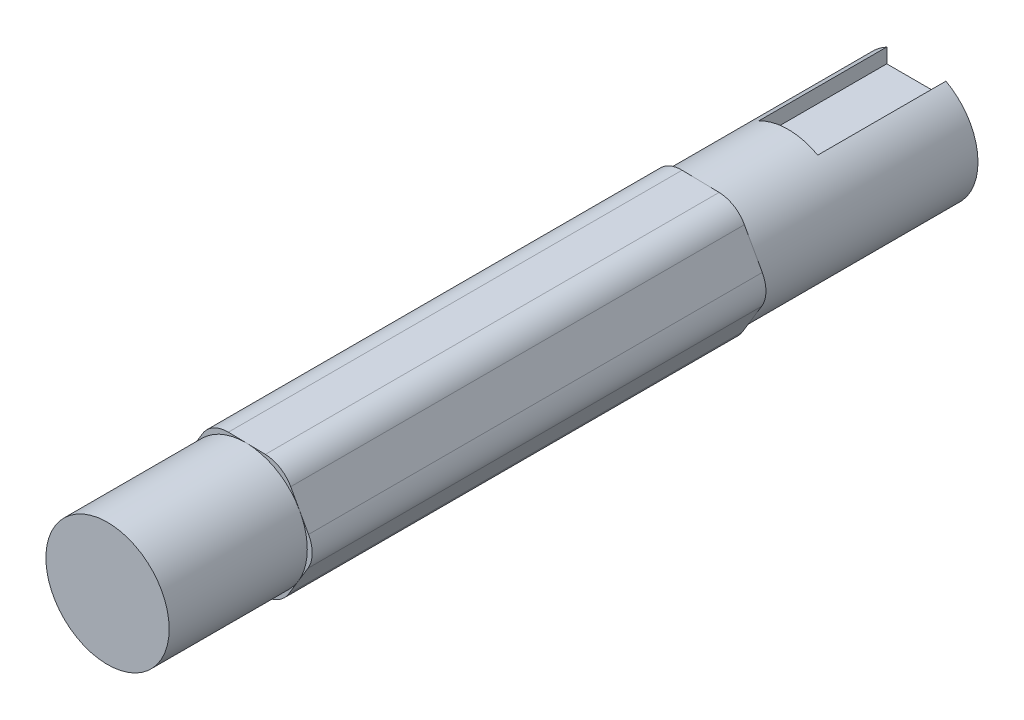
SolidWorks part; units mm, degrees
ref_plane "Front Plane" through (0, 0, 0) normal (0, 0, 1) x (1, 0, 0)
ref_plane "Top Plane" through (0, 0, 0) normal (0, 1, 0) x (1, 0, 0)
ref_plane "Right Plane" through (0, 0, 0) normal (1, 0, 0) x (0, 0, -1)
sketch "Sketch1" plane through (0, 0, 0) normal (0, 0, 1) x (1, 0, 0)
  circle A0 centre (0, 0) radius 6.25
  dimension "D1" = 12.5
extrude "Boss-Extrude1" add sketch "Sketch1" along normal blind 37 and the other way blind 45
sketch "Sketch3" plane through (0, 0, 0) normal (0, 1, 0) x (1, 0, 0)
  line L0 (-27.349, 0) -> (27.9883, 0) construction
  line L1 (-27.349, 31) -> (27.9883, 31) construction
  line L2 (-27.349, 32) -> (27.9883, 32) construction
  line L3 (-27.349, 42) -> (27.9883, 42) construction
  line L4 (27.9883, 45) -> (-27.349, 45) construction
  line L5 (-27.349, -31) -> (27.9883, -31) construction
  line L6 (-27.349, -37) -> (27.9883, -37) construction
  dimension "D1" = 31
  dimension "D2" = 1
  dimension "D3" = 10
  dimension "D4" = 3
  dimension "D5" = 31
  dimension "D6" = 6
sketch "Sketch4" plane through (0, 0, -45) normal (0, 0, -1) x (-1, 0, 0)
  line L0 (-18.2857, 6.25) -> (18.9059, 6.25) construction
  line L1 (-3, 8.5) -> (3, 8.5)
  line L2 (-3, 8.5) -> (-3, 4)
  line L3 (-3, 4) -> (3, 4)
  line L4 (3, 8.5) -> (3, 4)
  line L5 (0, 15.7597) -> (0, -12.3933) construction
  circle A0 centre (0, 0) radius 6.25 construction
  dimension "D1" = 6
  dimension "D2" = 4.5
extrude "Cut-Extrude1" cut sketch "Sketch4" against normal blind 13
ref_plane "Plane1" through (0, 0, 23) normal (0, 0, 1) x (1, 0, 0)
ref_plane "Plane2" through (0, 0, -23) normal (0, 0, 1) x (1, 0, 0)
sketch "Sketch5" plane through (0, 0, -23) normal (0, 0, 1) x (1, 0, 0)
  line L1 (3.7329, 6.1765) -> (-3.4825, 6.321)
  line L2 (-3.4825, 6.321) -> (-7.2154, 0.1445)
  line L3 (-7.2154, 0.1445) -> (-3.7329, -6.1765)
  line L4 (-3.7329, -6.1765) -> (3.4825, -6.321)
  line L5 (3.4825, -6.321) -> (7.2154, -0.1445)
  line L6 (7.2154, -0.1445) -> (3.7329, 6.1765)
  circle A0 centre (0, 0) radius 6.25 construction
  dimension "D1" = 12.5
extrude "Boss-Extrude2" add sketch "Sketch5" along normal up to surface (46 mm away) up to plane "Plane1"
fillet "Fillet1" radius 3 6 edges at (-3.4825, 6.321, 0) (-7.2154, 0.1445, 0) (-3.7329, -6.1765, 0) (3.4825, -6.321, 0) (7.2154, -0.1445, 0) (3.7329, 6.1765, 0)
